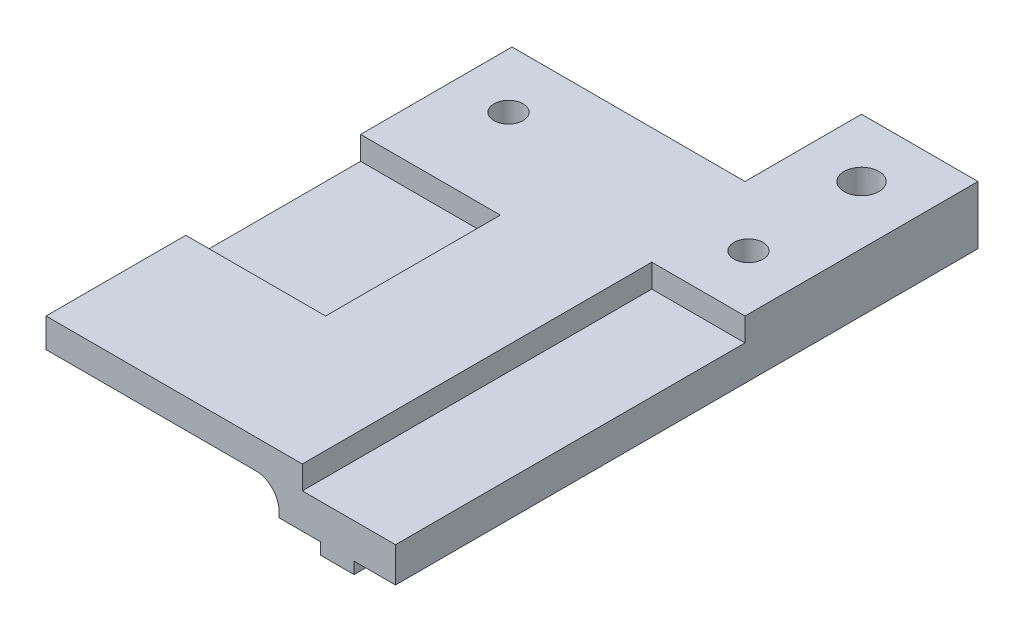
SolidWorks part; units mm, degrees
ref_plane "Front Plane" through (0, 0, 0) normal (0, 0, 1) x (1, 0, 0)
ref_plane "Top Plane" through (0, 0, 0) normal (0, 1, 0) x (1, 0, 0)
ref_plane "Right Plane" through (0, 0, 0) normal (1, 0, 0) x (0, 0, -1)
sketch "Sketch1" plane through (0, 0, 0) normal (0, 0, 1) x (1, 0, 0)
  line L1 (15, 0) -> (15, -5)
  line L2 (15, -5) -> (11.45, -5)
  line L3 (11.45, -5) -> (11.45, -6)
  line L4 (11.45, -6) -> (8.55, -6)
  line L5 (8.55, -6) -> (8.55, -5)
  line L6 (8.55, -5) -> (5, -5)
  line L7 (5, -5) -> (5, -2.5)
  line L8 (5, -2.5) -> (-15, -2.5)
  line L9 (-15, -2.5) -> (-15, 0)
  line L11 (15, 0) -> (-15, 0)
  point P0 (0, 0)
  point P12 (0, 0)
  point P13 (15, -0.2166)
  point P14 (-7.6455, -1.5291)
  point P16 (3.5693, -5.3613)
  point P17 (3.5097, -3)
  point P18 (14.0123, -5.5)
  dimension "D1" = 2.9
  dimension "D2" = 10
  dimension "D3" = 1
  dimension "D4" = 2.5
  dimension "D5" = 2.5
  dimension "D6" = 30
extrude "Boss-Extrude1" add sketch "Sketch1" along normal blind 50
sketch "Sketch2" plane through (0, 0, 0) normal (0, 1, 0) x (1, 0, 0)
  line L0 (-10.3, -15) -> (10.3, -15) construction
  line L1 (15, -50) -> (-15, -50) construction
  circle A0 centre (-10.3, -15) radius 1.25
  circle A1 centre (10.3, -15) radius 1.25
  point P4 (0, -15)
  dimension "D2" = 2.5
  dimension "D1" = 20.6
  dimension "D3" = 35
extrude "Cut-Extrude1" cut sketch "Sketch2" against normal through all
sketch "Sketch3" plane through (0, 0, 0) normal (0, 1, 0) x (1, 0, 0)
  line L0 (-15, -50) -> (-15, 0) construction
  line L1 (7, -20) -> (15, -20)
  line L2 (7, -20) -> (7, -50)
  line L3 (7, -50) -> (15, -50)
  line L4 (15, -20) -> (15, -50)
  line L5 (-15, -23) -> (-3, -23)
  line L6 (-15, -23) -> (-15, -38)
  line L7 (-15, -38) -> (-3, -38)
  line L8 (-3, -23) -> (-3, -38)
  line L10 (15, -50) -> (-15, -50) construction
  point P4 (-15, -23.0042)
  point P14 (15, -50)
  dimension "D1" = 8
  dimension "D2" = 30
  dimension "D3" = 12
  dimension "D4" = 15
  dimension "D5" = 12
extrude "Cut-Extrude2" cut sketch "Sketch3" against normal blind 2
sketch "Sketch4" plane through (0, -6, 0) normal (0, -1, 0) x (-1, 0, 0)
  line L0 (-8.55, 0) -> (-11.45, 0) construction
  line L1 (15, -50) -> (15, 0) construction
  line L2 (15, -10) -> (-5, -10)
  line L3 (15, -10) -> (15, 0)
  line L4 (15, 0) -> (-5, 0)
  line L5 (-5, -10) -> (-5, 0)
  line L6 (15, 0) -> (-5, 0) construction
  line L7 (-5, -50) -> (-5, 0) construction
  circle A0 centre (-10, -5) radius 1.5
  point P4 (-10, 0)
  point P13 (-4, -11.5301)
  dimension "D1" = 3
  dimension "D2" = 5
  dimension "D3" = 10
extrude "Cut-Extrude3" cut sketch "Sketch4" against normal through all
fillet "Fillet1" radius 2 1 edges at (5, -2.5, 30)
